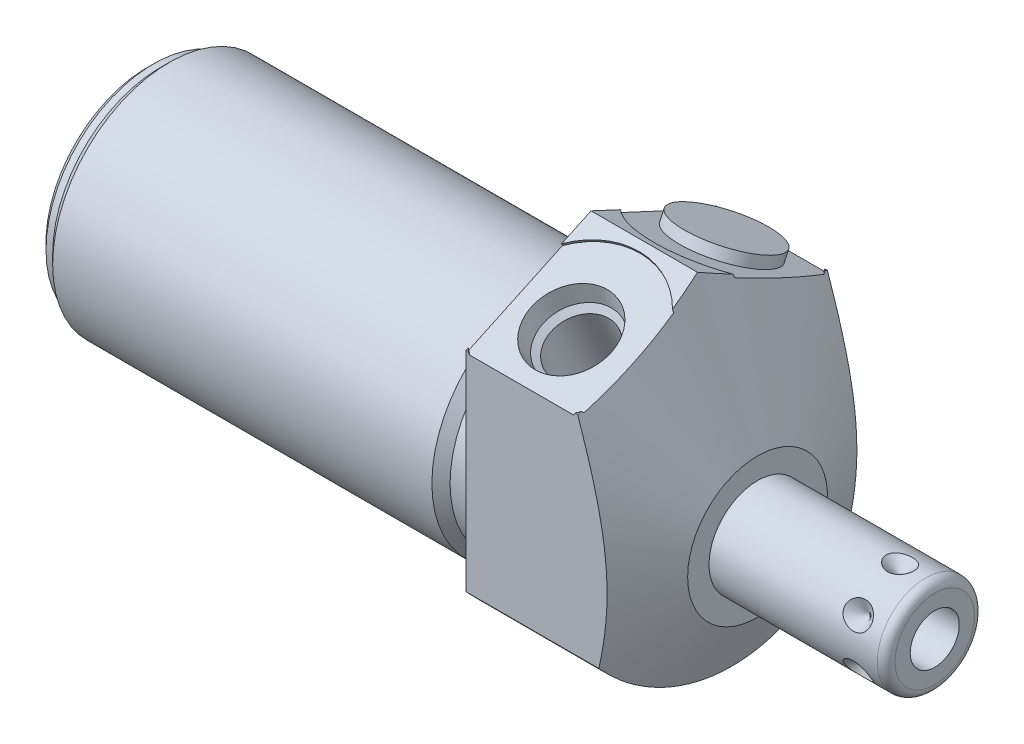
SolidWorks part; units mm, degrees
material "Alloy Steel"
ref_plane "Front Plane" through (0, 0, 0) normal (0, 0, 1) x (1, 0, 0)
ref_plane "Top Plane" through (0, 0, 0) normal (0, 1, 0) x (1, 0, 0)
ref_plane "Right Plane" through (0, 0, 0) normal (1, 0, 0) x (0, 0, -1)
ref_plane "Plane1" through (0, 0, 0) normal (1, 0, 0) x (0, 0, -1)
sketch "Sketch1" plane through (0, 0, 0) normal (1, 0, 0) x (0, 0, -1)
  circle A0 centre (0, 0) radius 19.05
  dimension "D1" = 38.1
extrude "Extrude1" add sketch "Sketch1" along normal blind 19.05 and the other way blind 50.8
ref_plane "Plane2" through (0, 0, 0) normal (1, 0, 0) x (0, 0, -1)
sketch "Sketch2" plane through (0, 0, 0) normal (1, 0, 0) x (0, 0, -1)
  line L0 (-14.6964, -4.7498) -> (14.6964, -4.7498) construction
  circle A0 centre (0, -4.7498) radius 13.3604
  circle A1 centre (0, 0) radius 19.05 construction
  circle A2 centre (0, 0) radius 19.05
  dimension "D1" = 26.7208
  dimension "D2" = 4.7498
extrude "Cut-Extrude1" cut sketch "Sketch2" against normal up to next
ref_plane "Plane4" through (0, 0, 0) normal (-1, 0, 0) x (0, 0, 1)
sketch "Sketch4" plane through (0, 0, 0) normal (-1, 0, 0) x (0, 0, 1)
  line L0 (14.2875, -12.6004) -> (14.2875, 11.3448)
  line L1 (14.2875, 11.3448) -> (0, 18.0071)
  line L2 (-14.2875, -12.6004) -> (-14.2875, 11.3448)
  line L3 (-14.2875, 11.3448) -> (0, 18.0071)
  line L4 (0, -20.9029) -> (0, 19.86) construction
  circle A0 centre (0, 0) radius 19.05 construction
  arc A1 (14.2875, -12.6004) -> (-14.2875, -12.6004) centre (0, 0) ccw
  dimension "D1" = 28.575
  dimension "D2" = 65
  dimension "D3" = 11.3448
extrude "Cut-Extrude3" cut sketch "Sketch4" against normal up to next
ref_plane "Plane6" through (0, 0, 0) normal (0, 0, 1) x (1, 0, 0)
sketch "Sketch6" plane through (0, 0, 0) normal (0, 0, 1) x (1, 0, 0)
  line L0 (12.1692, 18.0071) -> (19.05, 3.2512)
  line L1 (1.9872, -4.7498) -> (19.8625, -4.7498) construction
  line L2 (-50.8, -4.7498) -> (0, -4.7498) construction
  line L3 (19.05, 18.0071) -> (19.05, 11.3448) construction
  line L4 (19.05, 3.2512) -> (19.05, 18.0071)
  line L5 (19.05, 18.0071) -> (12.1692, 18.0071)
  line L6 (19.05, 18.0071) -> (0, 18.0071) construction
  dimension "D1" = 8.001
  dimension "D2" = 25
revolve "Cut-Revolve2" cut sketch "Sketch6" angle 360 about L1
ref_plane "Plane7" through (6.35, 13.7124, 8.6091) normal (1, 0, 0) x (0, 0.4226, -0.9063)
sketch "S2D0002" plane through (6.35, 13.7124, 8.6091) normal (1, 0, 0) x (0, 0.4226, -0.9063)
  line L0 (0, 0) -> (4.5466, 0)
  line L1 (4.5466, 0) -> (4.1066, -2.0701)
  line L2 (4.1066, -2.0701) -> (3.4544, -2.7223)
  line L3 (3.4544, -2.7223) -> (3.4544, -12.192)
  line L4 (3.4544, -12.192) -> (0, -12.192)
  line L5 (0, -12.192) -> (0, 0)
  line L6 (0, -12.8016) -> (0, 0.6096) construction
  dimension "D1" = 12.192
revolve "Cut-Revolve3" cut sketch "S2D0002" angle 360 about L6
ref_plane "Plane8" through (6.35, 13.7124, -8.6091) normal (1, 0, 0) x (0, -0.4226, -0.9063)
sketch "Sketch19" plane through (0, 14.791, 6.8971) normal (0, 0.9063, 0.4226) x (1, 0, 0)
  circle A0 centre (6.35, -2.0074) radius 8.6614
  dimension "D1" = 17.3228
extrude "Cut-Extrude4" cut sketch "Sketch19" against normal blind 0.254
sketch "Sketch8" plane through (6.35, 13.7124, -8.6091) normal (1, 0, 0) x (0, -0.4226, -0.9063)
  line L0 (0, 0) -> (4.5466, 0)
  line L1 (4.5466, 0) -> (4.1066, -2.0701)
  line L2 (4.1066, -2.0701) -> (3.4544, -2.7223)
  line L3 (3.4544, -2.7223) -> (3.4544, -12.192)
  line L4 (3.4544, -12.192) -> (0, -12.192)
  line L5 (0, -12.192) -> (0, 0)
  line L6 (0, -12.8016) -> (0, 0.6096) construction
  dimension "D1" = 12.192
revolve "Cut-Revolve4" cut sketch "Sketch8" angle 360 about L6
sketch "Sketch20" plane through (0, 14.791, -6.8971) normal (0, 0.9063, -0.4226) x (1, 0, 0)
  circle A0 centre (6.35, 2.0074) radius 8.6614
  dimension "D1" = 17.3228
extrude "Cut-Extrude5" cut sketch "Sketch20" against normal blind 0.254
ref_plane "Plane10" through (0, 0, 0) normal (0, 0, 1) x (1, 0, 0)
sketch "Sketch10" plane through (0, 0, 0) normal (0, 0, 1) x (1, 0, 0)
  line L0 (0, 8.6106) -> (0, 7.5692)
  line L1 (0, 7.5692) -> (-3.81, 7.5692)
  line L2 (-3.81, 7.5692) -> (-4.8514, 8.6106)
  line L3 (-5.094, -4.7498) -> (0.2426, -4.7498) construction
  line L4 (0, 8.6106) -> (-4.8514, 8.6106)
  line L5 (-50.8, -4.7498) -> (0, -4.7498) construction
  line L6 (0, 8.6106) -> (-50.8, 8.6106) construction
  line L7 (0, 11.3448) -> (0, -12.6004) construction
  dimension "D1" = 24.638
  dimension "D2" = 3.81
  dimension "D3" = 45
revolve "Cut-Revolve6" cut sketch "Sketch10" angle 360 about L3
ref_plane "Plane12" through (0, 0, 0) normal (0, 0, 1) x (1, 0, 0)
sketch "Sketch12" plane through (0, 0, 0) normal (0, 0, 1) x (1, 0, 0)
  line L0 (-50.8, 8.6106) -> (-50.8, 7.5692)
  line L1 (-50.8, 7.5692) -> (-49.276, 7.5692)
  line L2 (-49.276, 7.5692) -> (-48.2346, 8.6106)
  line L3 (-50.9283, -4.7498) -> (-48.1063, -4.7498) construction
  line L4 (-50.8, 8.6106) -> (-48.2346, 8.6106)
  line L5 (-50.8, -4.7498) -> (-4.8514, -4.7498) construction
  line L6 (-4.8514, 8.6106) -> (-50.8, 8.6106) construction
  line L7 (-50.8, 8.6106) -> (-50.8, -18.1102) construction
  dimension "D1" = 24.638
  dimension "D2" = 1.524
  dimension "D3" = 45
revolve "Cut-Revolve8" cut sketch "Sketch12" angle 360 about L3
chamfer "Chamfer1" distance 0.762 angle 45 1 edges at (-50.8, -4.7498, 12.319)
ref_plane "Plane13" through (0, 0, 0) normal (0, 0, 1) x (0, -1, 0)
sketch "Sketch13" plane through (0, 0, 0) normal (0, 0, 1) x (0, -1, 0)
  line L0 (4.7498, 19.05) -> (4.7498, 39.3192)
  line L1 (4.7498, 39.3192) -> (9.2901, 39.3192)
  line L2 (10.306, 38.3032) -> (10.306, 19.05)
  line L3 (10.306, 19.05) -> (4.7498, 19.05)
  line L4 (4.7498, 18.0365) -> (4.7498, 40.3327) construction
  line L5 (4.7498, -48.2346) -> (4.7498, -4.8514) construction
  line L6 (12.7508, 19.05) -> (-3.2512, 19.05) construction
  line L7 (-11.3448, 0) -> (12.6004, 0) construction
  arc A0 (10.306, 38.3032) -> (9.2901, 39.3192) centre (9.2901, 38.3032) ccw
  dimension "D2" = 1.016
  dimension "D1" = 39.3192
  dimension "D3" = 11.1125
revolve "Revolve1" add sketch "Sketch13" angle 360 about L4
ref_plane "Plane14" through (39.3192, -7.5565, 0) normal (0, 0, 1) x (0, -1, 0)
sketch "S2D0001" plane through (39.3192, -7.5565, 0) normal (0, 0, 1) x (0, -1, 0)
  line L0 (0, 0) -> (0, -10.16)
  line L1 (0, -10.16) -> (-2.8067, -11.8464)
  line L2 (0, 0) -> (-2.8067, 0)
  line L3 (-2.8067, 0) -> (-2.8067, -11.8464)
  line L4 (-2.8067, -12.4388) -> (-2.8067, 0.5923) construction
  line L5 (-2.8067, -1.016) -> (-2.8067, -20.2692) construction
  line L6 (1.7336, 0) -> (-7.347, 0) construction
  dimension "D1" = 5.6134
  dimension "D2" = 59
  dimension "D3" = 10.16
revolve "Cut-Revolve9" cut sketch "S2D0001" angle 360 about L4
ref_plane "Plane15" through (19.05, 14.5608, -6.7898) normal (0, -0.9063, 0.4226) x (0, -0.4226, -0.9063)
sketch "Sketch15" plane through (19.05, 14.5608, -6.7898) normal (0, -0.9063, 0.4226) x (0, -0.4226, -0.9063)
  circle A0 centre (2.0074, -12.7) radius 5.3086
extrude "Extrude2" add sketch "Sketch15" against normal blind 1.27
ref_plane "Plane16" through (35.3568, -10.306, 0) normal (0, 0, 1) x (-1, 0, 0)
ref_plane "Plane17" through (0, -3.5624, -2.0567) normal (0, 0.866, 0.5) x (-1, 0, 0)
sketch "Sketch16" plane through (35.3568, 0.8065, 0) normal (0, 0, -1) x (-1, 0, 0)
  line L0 (0, 0) -> (1.5875, 0)
  line L1 (1.5875, 0) -> (0, -1.5875)
  line L2 (0, 0) -> (0, -1.5875)
  line L3 (0, -3.4788) -> (0, 0.0794) construction
  line L4 (-3.9624, -1.016) -> (-3.9624, -10.0965) construction
  line L5 (16.3068, 0) -> (-2.9464, 0) construction
  dimension "D1" = 3.9624
  dimension "D2" = 3.175
  dimension "D3" = 45
revolve "Cut-Revolve10" cut sketch "Sketch16" angle 360 about L3
pattern_circular "CirPattern1" count 6 over 360 about axis through (18.0365, -4.7498, 0) along (-1, 0, 0) of "Cut-Revolve10"
